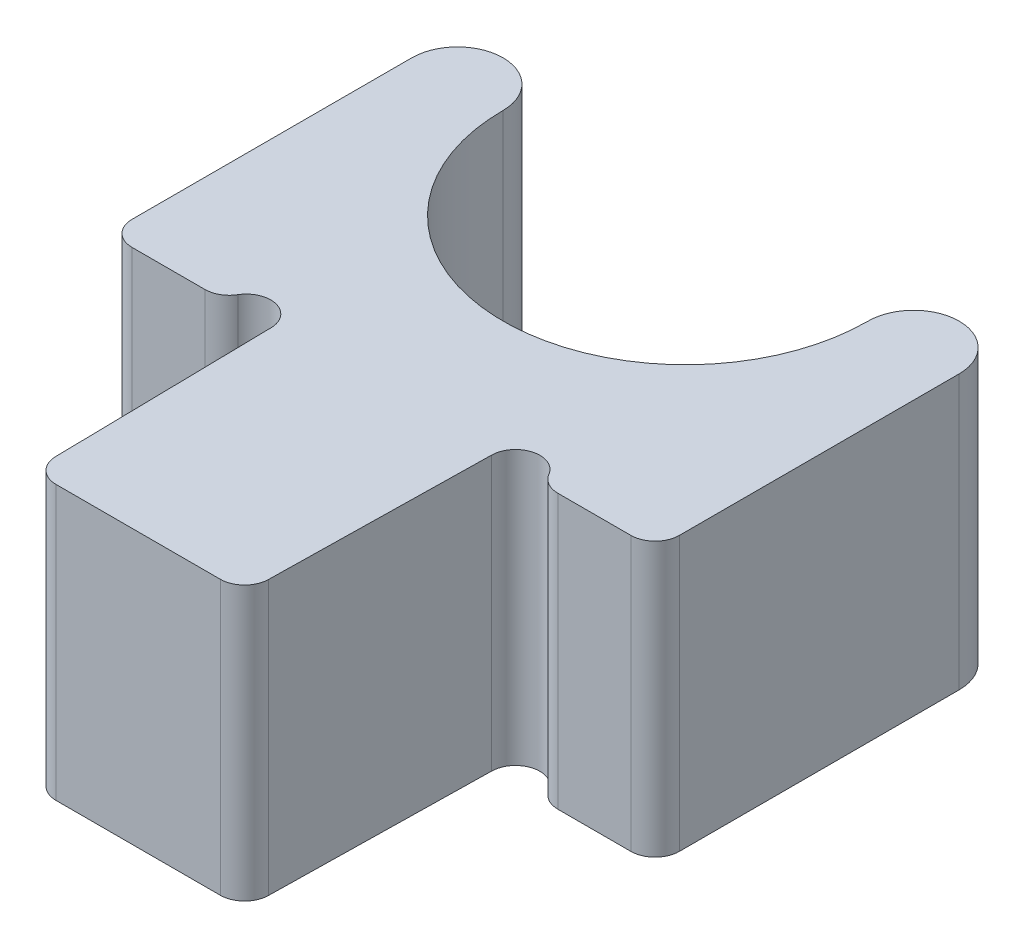
SolidWorks part; units mm, degrees
ref_plane "Front Plane" through (0, 0, 0) normal (0, 0, 1) x (1, 0, 0)
ref_plane "Top Plane" through (0, 0, 0) normal (0, 1, 0) x (1, 0, 0)
ref_plane "Right Plane" through (0, 0, 0) normal (1, 0, 0) x (0, 0, -1)
sketch "Sketch1" plane through (0, 0, 0) normal (0, 1, 0) x (1, 0, 0)
  line L0 (0, 0) -> (0, -12.2292) construction
  line L1 (-4.5, 0) -> (-4.5, -4.6)
  line L2 (4.5, 0) -> (4.5, -4.6)
  line L3 (2.9016, -5) -> (4.1, -5)
  line L4 (1.813, -5) -> (1.75, -8.607)
  line L5 (1.3501, -9) -> (-1.3501, -9)
  line L6 (-2.9016, -5) -> (-4.1, -5)
  line L7 (-1.813, -5) -> (-1.75, -8.607)
  arc A0 (-3, 0) -> (3, 0) centre (0, 0) ccw
  arc A1 (3, 0) -> (4.5, 0) centre (3.75, 0) cw
  arc A2 (-3, 0) -> (-4.5, 0) centre (-3.75, 0) ccw
  arc A3 (-4.5, -4.6) -> (-4.1, -5) centre (-4.1, -4.6) ccw
  arc A4 (1.75, -8.607) -> (1.3501, -9) centre (1.3501, -8.6) cw
  arc A5 (-2.5573, -4.8035) -> (-2.9016, -5) centre (-2.9016, -4.6) cw
  arc A6 (4.5, -4.6) -> (4.1, -5) centre (4.1, -4.6) cw
  arc A7 (1.813, -5) -> (2.5573, -4.8035) centre (2.2129, -5.007) cw
  arc A8 (2.5573, -4.8035) -> (2.9016, -5) centre (2.9016, -4.6) ccw
  arc A9 (-1.813, -5) -> (-2.5573, -4.8035) centre (-2.2129, -5.007) ccw
  arc A10 (-1.75, -8.607) -> (-1.3501, -9) centre (-1.3501, -8.6) ccw
  point P26 (0, -9)
  dimension "D1" = 3
  dimension "D2" = 0.75
  dimension "D6" = 4
  dimension "D3" = 5
  dimension "D7" = 0.4
  dimension "D4" = 1
  dimension "D5" = 1.75
extrude "Boss-Extrude1" add sketch "Sketch1" along normal blind 4.5
